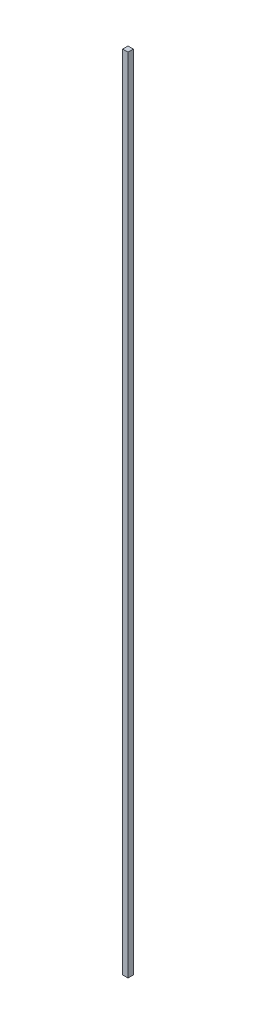
SolidWorks part; units mm, degrees
ref_plane "Front Plane" through (0, 0, 0) normal (0, 0, 1) x (1, 0, 0)
ref_plane "Top Plane" through (0, 0, 0) normal (0, 1, 0) x (1, 0, 0)
ref_plane "Right Plane" through (0, 0, 0) normal (1, 0, 0) x (0, 0, -1)
sketch "Sketch1" plane through (0, 0, 0) normal (0, 1, 0) x (1, 0, 0)
  line L1 (-5, -5) -> (5, -5)
  line L2 (-5, -5) -> (-5, 5)
  line L3 (-5, 5) -> (5, 5)
  line L4 (5, -5) -> (5, 5)
  line L5 (-5, -5) -> (5, 5) construction
  line L6 (-5, 5) -> (5, -5) construction
  point P0 (0, 0)
  dimension "D1" = 10
  dimension "D2" = 10
extrude "Boss-Extrude1" add sketch "Sketch1" along normal blind 1500
